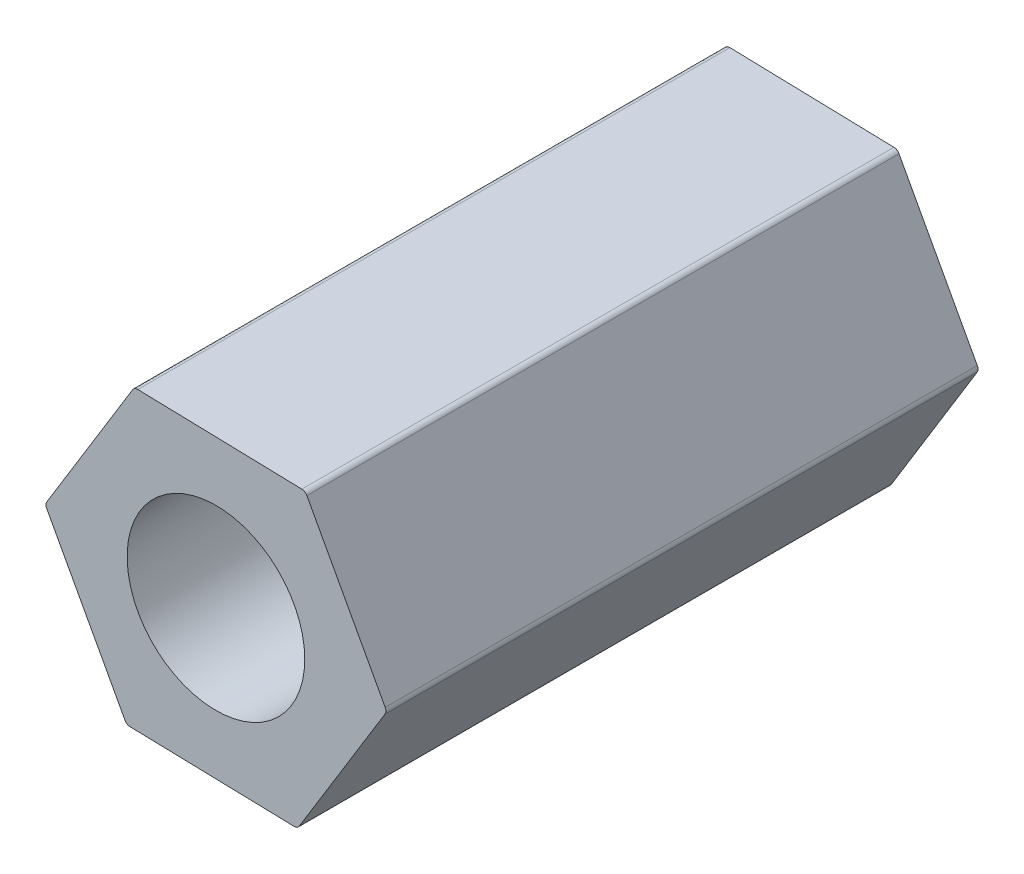
SolidWorks part; units mm, degrees
ref_plane "Front Plane" through (0, 0, 0) normal (0, 0, 1) x (1, 0, 0)
ref_plane "Top Plane" through (0, 0, 0) normal (0, 1, 0) x (1, 0, 0)
ref_plane "Right Plane" through (0, 0, 0) normal (1, 0, 0) x (0, 0, -1)
sketch "Sketch1" plane through (0, 0, 0) normal (0, 0, 1) x (1, 0, 0)
  line L1 (1.5084, 2.4613) -> (-1.3774, 2.537)
  line L2 (-1.3774, 2.537) -> (-2.8858, 0.0756)
  line L3 (-2.8858, 0.0756) -> (-1.5084, -2.4613)
  line L4 (-1.5084, -2.4613) -> (1.3774, -2.537)
  line L5 (1.3774, -2.537) -> (2.8858, -0.0756)
  line L6 (2.8858, -0.0756) -> (1.5084, 2.4613)
  circle A0 centre (0, 0) radius 2.5 construction
  circle A1 centre (0, 0) radius 1.5 construction
  dimension "D1" = 5
  dimension "D2" = 3
extrude "Boss-Extrude1" add sketch "Sketch1" along normal blind 10
sketch "Sketch3" plane through (0, 0, 10) normal (0, 0, 1) x (1, 0, 0)
  circle A0 centre (0, 0) radius 1.5
  dimension "D1" = 3
hole_wizard "M3 Tapped Hole1" positions "3DSketch4" profile "Sketch5" tap size "M3" standard "GB" end condition through all
sketch3d "3DSketch4"
  point P0 (0, 0, 10)
sketch "Sketch5" plane through (0, 0, 10) normal (1, 0, 0) x (0, -1, 0)
  line L0 (0, 0) -> (0, 10)
  line L1 (0, 10) -> (1.5, 10)
  line L2 (1.5, 10) -> (1.5, 0)
  line L5 (1.5, 0) -> (0, 0)
  line L11 (0, -6.35) -> (0, 107.95) construction
  dimension "Thru Tap Drill Dia." = 3
  dimension "Thru Tap Drill Depth" = 10
cosmetic thread "Hole Thread1" parameters "D2"=3
fillet "Fillet1" radius 0.1 6 edges at (-1.3774, 2.537, 5) (-2.8858, 0.0756, 5) (-1.5084, -2.4613, 5) (1.3774, -2.537, 5) (2.8858, -0.0756, 5) (1.5084, 2.4613, 5)
